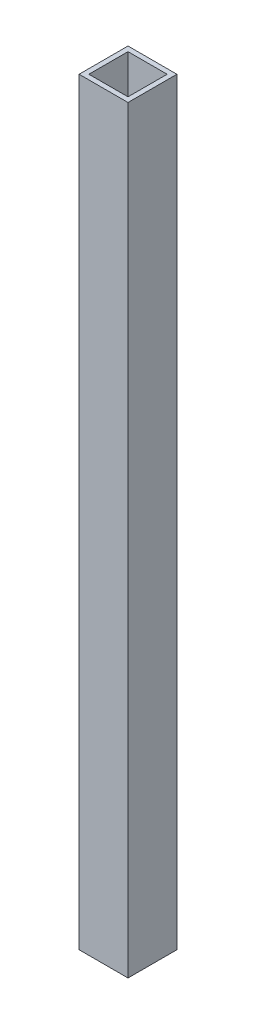
SolidWorks part; units mm, degrees
ref_plane "前视基准面" through (0, 0, 0) normal (0, 0, 1) x (1, 0, 0)
ref_plane "上视基准面" through (0, 0, 0) normal (0, 1, 0) x (1, 0, 0)
ref_plane "右视基准面" through (0, 0, 0) normal (1, 0, 0) x (0, 0, -1)
ref_plane "基准面4" through (0, -155, 0) normal (0, -1, 0) x (1, 0, 0)
sketch "草图1" plane through (0, -155, 0) normal (0, -1, 0) x (1, 0, 0)
  line L0 (45, -5) -> (45, 5)
  line L1 (45, 5) -> (35, 5)
  line L2 (35, 5) -> (35, -5)
  line L3 (35, -5) -> (45, -5)
  line L4 (44, 4) -> (44, -4)
  line L5 (44, -4) -> (36, -4)
  line L6 (36, -4) -> (36, 4)
  line L7 (36, 4) -> (44, 4)
extrude "凸台-拉伸1" add sketch "草图1" against normal blind 155
